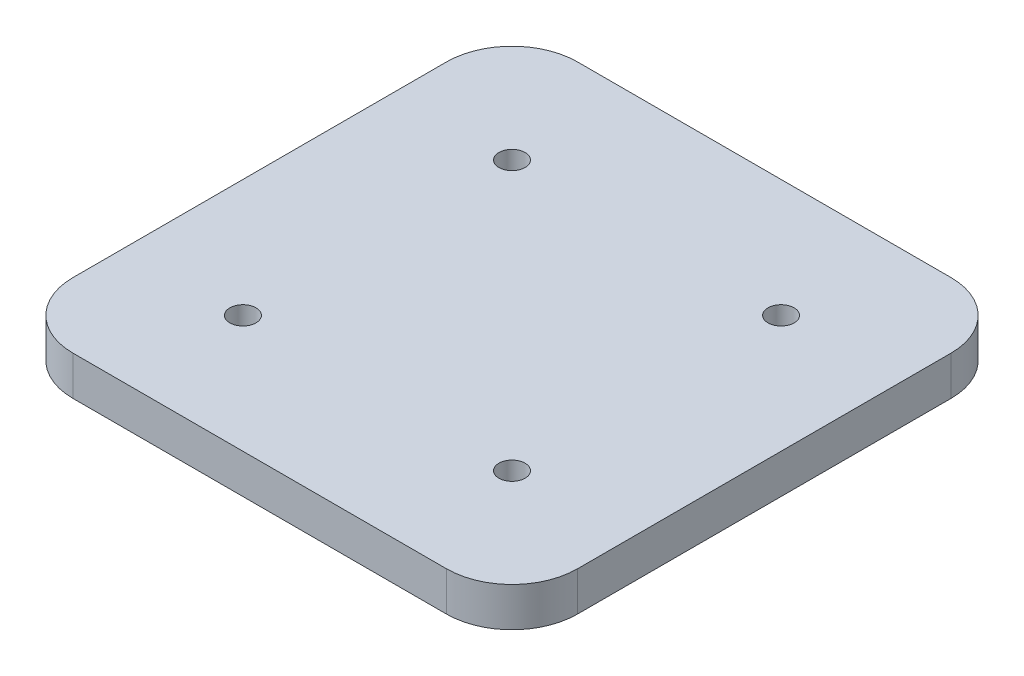
SolidWorks part; units mm, degrees
ref_plane "Front Plane" through (0, 0, 0) normal (0, 0, 1) x (1, 0, 0)
ref_plane "Top Plane" through (0, 0, 0) normal (0, 1, 0) x (1, 0, 0)
ref_plane "Right Plane" through (0, 0, 0) normal (1, 0, 0) x (0, 0, -1)
ref_plane "Plano1" through (0, 65.5, 0) normal (0, -1, 0) x (1, 0, 0)
sketch "Croquis1" plane through (0, 65.5, 0) normal (0, -1, 0) x (1, 0, 0)
  line L0 (25.419, -77.17) -> (102.569, -77.17)
  line L1 (102.569, -77.17) -> (102.569, -0.02)
  line L2 (102.569, -0.02) -> (25.419, -0.02)
  line L3 (25.419, -0.02) -> (25.419, -77.17)
  dimension "D1" = 77.15
  dimension "D2" = 77.15
  dimension "D3" = 25.419
  dimension "D4" = 77.17
extrude "Saliente-Extruir1" add sketch "Croquis1" against normal blind 6
sketch "Croquis2" plane through (0, 71.5, 0) normal (0, 1, 0) x (1, 0, 0)
  line L0 (102.569, 77.17) -> (102.569, 0.02) construction
  line L1 (25.419, 77.17) -> (102.569, 77.17) construction
  line L2 (25.419, 0.02) -> (25.419, 77.17) construction
  line L3 (102.569, 0.02) -> (25.419, 0.02) construction
  circle A0 centre (84.569, 59.17) radius 2
  circle A1 centre (84.569, 18.02) radius 2
  circle A2 centre (43.419, 18.02) radius 2
  circle A3 centre (43.419, 59.17) radius 2
  dimension "D1" = 4
  dimension "D2" = 4
  dimension "D3" = 4
  dimension "D4" = 4
  dimension "D7" = 18
  dimension "D12" = 18
  dimension "D5" = 18
  dimension "D6" = 18
  dimension "D8" = 18
  dimension "D9" = 18
  dimension "D10" = 18
  dimension "D11" = 18
extrude "Cortar-Extruir1" cut sketch "Croquis2" against normal blind 40
fillet "Redondeo1" radius 10 4 edges at (102.569, 68.5, -0.02) (102.569, 68.5, -77.17) (25.419, 68.5, -77.17) (25.419, 68.5, -0.02)
